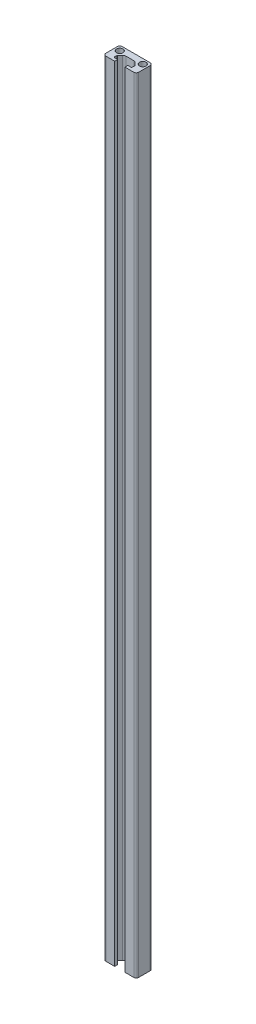
SolidWorks part; units mm, degrees
ref_plane "Front Plane" through (0, 0, 0) normal (0, 0, 1) x (1, 0, 0)
ref_plane "Top Plane" through (0, 0, 0) normal (0, 1, 0) x (1, 0, 0)
ref_plane "Right Plane" through (0, 0, 0) normal (1, 0, 0) x (0, 0, -1)
ref_plane "Plane1" through (0, 238.5, 0) normal (0, 1, 0) x (1, 0, 0)
sketch "Sketch1" plane through (0, 238.5, 0) normal (0, 1, 0) x (1, 0, 0)
  line L0 (-3.1, 1.8) -> (-4.95, 1.8)
  line L1 (-5.45, 2.3) -> (-5.45, 3.6929)
  line L2 (-5.3036, 4.0464) -> (-3.8358, 5.5142)
  line L3 (-2.4216, 6.1) -> (2.4216, 6.1)
  line L4 (3.8358, 5.5142) -> (5.3036, 4.0464)
  line L5 (5.45, 3.6929) -> (5.45, 2.3)
  line L6 (4.95, 1.8) -> (3.1, 1.8)
  line L7 (3.1, 1.8) -> (3.1, 0)
  line L8 (3.1, 0) -> (8.5, 0)
  line L9 (10, 1.5) -> (10, 8.5)
  line L10 (8.5, 10) -> (-8.5, 10)
  line L11 (-10, 8.5) -> (-10, 1.5)
  line L12 (-8.5, 0) -> (-3.1, 0)
  line L13 (-3.1, 0) -> (-3.1, 1.8)
  arc A0 (-4.95, 1.8) -> (-5.45, 2.3) centre (-4.95, 2.3) cw
  arc A1 (-5.45, 3.6929) -> (-5.3036, 4.0464) centre (-4.95, 3.6929) cw
  arc A2 (-3.8358, 5.5142) -> (-2.4216, 6.1) centre (-2.4216, 4.1) cw
  arc A3 (2.4216, 6.1) -> (3.8358, 5.5142) centre (2.4216, 4.1) cw
  arc A4 (5.3036, 4.0464) -> (5.45, 3.6929) centre (4.95, 3.6929) cw
  arc A5 (5.45, 2.3) -> (4.95, 1.8) centre (4.95, 2.3) cw
  arc A6 (8.5, 0) -> (10, 1.5) centre (8.5, 1.5) ccw
  arc A7 (10, 8.5) -> (8.5, 10) centre (8.5, 8.5) ccw
  arc A8 (-8.5, 10) -> (-10, 8.5) centre (-8.5, 8.5) ccw
  arc A9 (-10, 1.5) -> (-8.5, 0) centre (-8.5, 1.5) ccw
  circle A10 centre (-7, 7) radius 2
  circle A11 centre (7, 7) radius 2
extrude "Boss-Extrude1" add sketch "Sketch1" against normal blind 477
